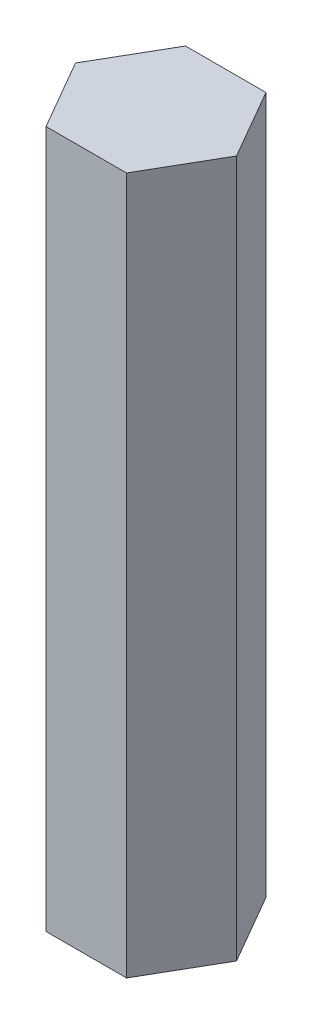
SolidWorks part; units mm, degrees
ref_plane "Front Plane" through (0, 0, 0) normal (0, 0, 1) x (1, 0, 0)
ref_plane "Top Plane" through (0, 0, 0) normal (0, 1, 0) x (1, 0, 0)
ref_plane "Right Plane" through (0, 0, 0) normal (1, 0, 0) x (0, 0, -1)
sketch "Sketch1" plane through (0, 0, 0) normal (0, 1, 0) x (1, 0, 0)
  line L1 (4.6188, 0) -> (2.3094, 4)
  line L2 (2.3094, 4) -> (-2.3094, 4)
  line L3 (-2.3094, 4) -> (-4.6188, 0)
  line L4 (-4.6188, 0) -> (-2.3094, -4)
  line L5 (-2.3094, -4) -> (2.3094, -4)
  line L6 (2.3094, -4) -> (4.6188, 0)
  circle A0 centre (0, 0) radius 4 construction
extrude "Boss-Extrude1" add sketch "Sketch1" along normal blind 40
